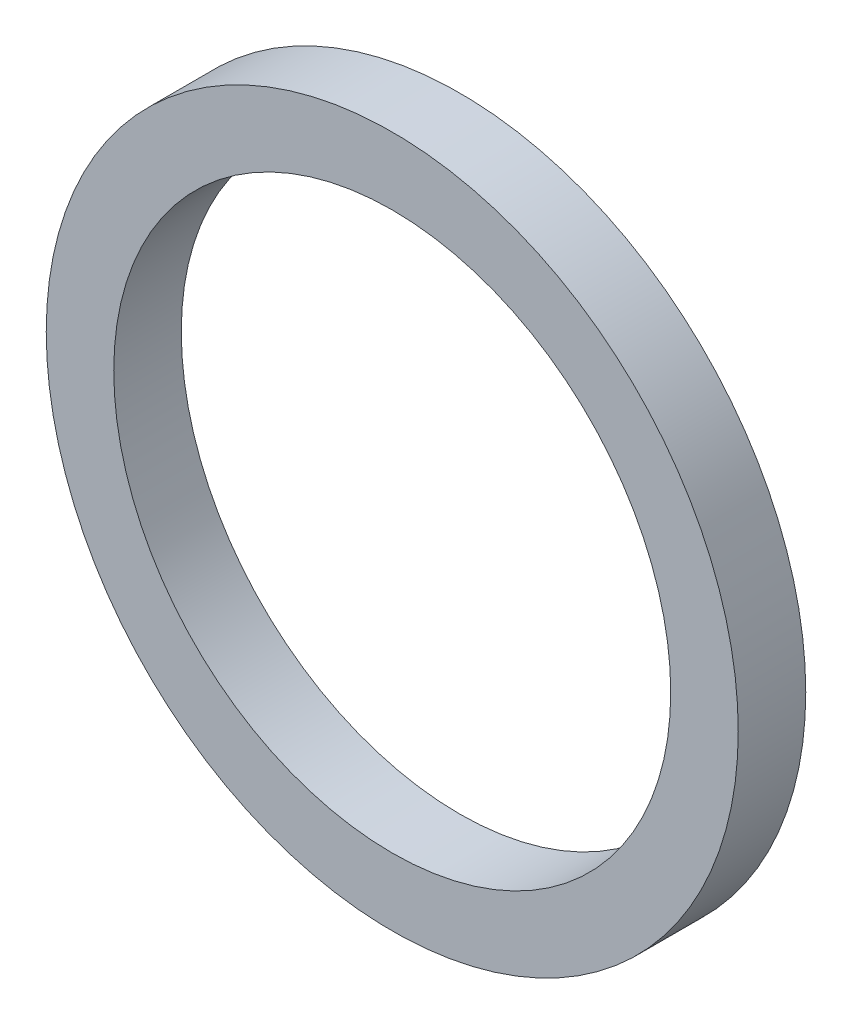
SolidWorks part; units mm, degrees
material "ABS"
ref_plane "正面" through (0, 0, 0) normal (0, 0, 1) x (1, 0, 0)
ref_plane "平面" through (0, 0, 0) normal (0, 1, 0) x (1, 0, 0)
ref_plane "右側面" through (0, 0, 0) normal (1, 0, 0) x (0, 0, -1)
sketch "ｽｹｯﾁ1" plane through (0, 0, 0) normal (0, 0, 1) x (1, 0, 0)
  circle A0 centre (0, 0) radius 10.25
  circle A1 centre (0, 0) radius 8.25
  dimension "D1" = 20.5
  dimension "D2" = 16.5
extrude "ﾎﾞｽ - 押し出し1" add sketch "ｽｹｯﾁ1" along normal blind 2
